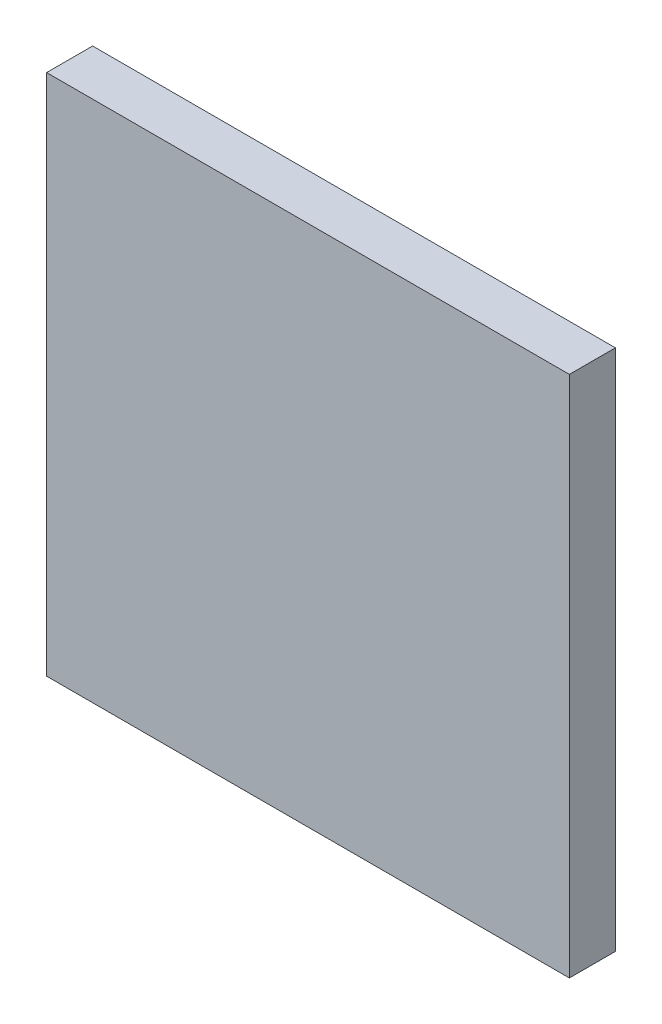
SolidWorks part; units mm, degrees
ref_plane "前视基准面" through (0, 0, 0) normal (0, 0, 1) x (1, 0, 0)
ref_plane "上视基准面" through (0, 0, 0) normal (0, 1, 0) x (1, 0, 0)
ref_plane "右视基准面" through (0, 0, 0) normal (1, 0, 0) x (0, 0, -1)
sketch "草图1" plane through (0, 0, 0) normal (0, 0, 1) x (1, 0, 0)
  line L1 (-6.25, -6.25) -> (6.25, -6.25)
  line L2 (-6.25, -6.25) -> (-6.25, 6.25)
  line L3 (-6.25, 6.25) -> (6.25, 6.25)
  line L4 (6.25, -6.25) -> (6.25, 6.25)
  line L5 (-6.25, -6.25) -> (6.25, 6.25) construction
  line L6 (-6.25, 6.25) -> (6.25, -6.25) construction
  circle A0 centre (0, 0) radius 6.25 construction
  dimension "D1" = 12.5
  dimension "D2" = 12.5
  dimension "D3" = 12.5
extrude "凸台-拉伸1" add sketch "草图1" along normal blind 1.1
